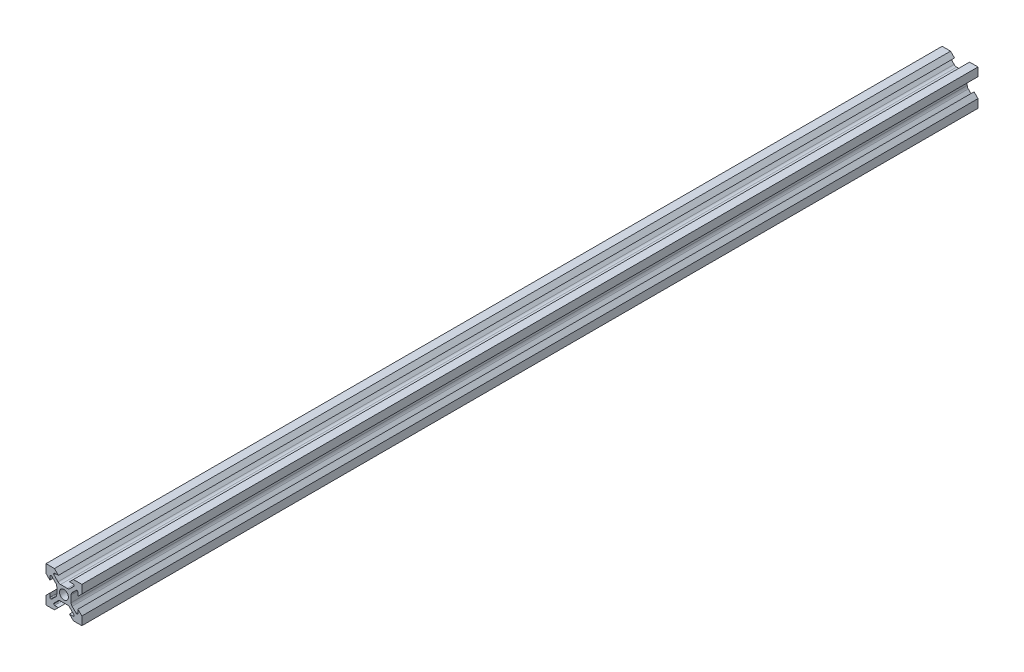
SolidWorks part; units mm, degrees
ref_plane "Front Plane" through (0, 0, 0) normal (0, 0, 1) x (1, 0, 0)
ref_plane "Top Plane" through (0, 0, 0) normal (0, 1, 0) x (1, 0, 0)
ref_plane "Right Plane" through (0, 0, 0) normal (1, 0, 0) x (0, 0, -1)
sketch "Sketch1" plane through (0, 0, 0) normal (0, 0, 1) x (1, 0, 0)
  line L0 (0, -10) -> (0, 10) construction
  line L1 (-10, 10) -> (10, 10) construction
  line L2 (-10, 10) -> (-10, -10) construction
  line L3 (-10, -10) -> (10, -10) construction
  line L4 (10, 10) -> (10, -10) construction
  line L5 (-10, 10) -> (10, -10) construction
  line L6 (-10, -10) -> (10, 10) construction
  line L7 (-10, 0) -> (10, 0) construction
  line L8 (-4, 0) -> (-4, 1.8988)
  line L9 (-4.5858, 3.313) -> (-6.8263, 5.5536)
  line L10 (-7.1799, 5.7) -> (-7.3, 5.7)
  line L11 (-7.8, 5.2) -> (-7.8, 3.1)
  line L12 (-7.8, 3.1) -> (-10, 5.3)
  line L13 (-10, 5.3) -> (-10, 10)
  line L14 (0, 4) -> (-1.8988, 4)
  line L15 (-3.313, 4.5858) -> (-5.5536, 6.8263)
  line L16 (-5.7, 7.1799) -> (-5.7, 7.3)
  line L17 (-5.2, 7.8) -> (-3.1, 7.8)
  line L18 (-3.1, 7.8) -> (-5.3, 10)
  line L19 (-5.3, 10) -> (-10, 10)
  line L20 (5.3, 10) -> (10, 10)
  line L21 (3.1, 7.8) -> (5.3, 10)
  line L22 (5.2, 7.8) -> (3.1, 7.8)
  line L23 (5.7, 7.1799) -> (5.7, 7.3)
  line L24 (3.313, 4.5858) -> (5.5536, 6.8263)
  line L25 (0, 4) -> (1.8988, 4)
  line L26 (10, -5.3) -> (10, -10)
  line L27 (7.8, -3.1) -> (10, -5.3)
  line L28 (7.8, -5.2) -> (7.8, -3.1)
  line L29 (7.1799, -5.7) -> (7.3, -5.7)
  line L30 (4.5858, -3.313) -> (6.8263, -5.5536)
  line L31 (4, 0) -> (4, -1.8988)
  line L32 (-5.3, -10) -> (-10, -10)
  line L33 (-3.1, -7.8) -> (-5.3, -10)
  line L34 (-5.2, -7.8) -> (-3.1, -7.8)
  line L35 (-5.7, -7.1799) -> (-5.7, -7.3)
  line L36 (-3.313, -4.5858) -> (-5.5536, -6.8263)
  line L37 (0, -4) -> (-1.8988, -4)
  line L38 (10, 5.3) -> (10, 10)
  line L39 (7.8, 3.1) -> (10, 5.3)
  line L40 (7.8, 5.2) -> (7.8, 3.1)
  line L41 (7.1799, 5.7) -> (7.3, 5.7)
  line L42 (4.5858, 3.313) -> (6.8263, 5.5536)
  line L43 (4, 0) -> (4, 1.8988)
  line L44 (5.3, -10) -> (10, -10)
  line L45 (3.1, -7.8) -> (5.3, -10)
  line L46 (5.2, -7.8) -> (3.1, -7.8)
  line L47 (5.7, -7.1799) -> (5.7, -7.3)
  line L48 (3.313, -4.5858) -> (5.5536, -6.8263)
  line L49 (0, -4) -> (1.8988, -4)
  line L50 (-10, -5.3) -> (-10, -10)
  line L51 (-7.8, -3.1) -> (-10, -5.3)
  line L52 (-7.8, -5.2) -> (-7.8, -3.1)
  line L53 (-7.1799, -5.7) -> (-7.3, -5.7)
  line L54 (-4.5858, -3.313) -> (-6.8263, -5.5536)
  line L55 (-4, 0) -> (-4, -1.8988)
  circle A0 centre (0, 0) radius 2.5
  arc A1 (-7.3, 5.7) -> (-7.8, 5.2) centre (-7.3, 5.2) ccw
  arc A2 (-6.8263, 5.5536) -> (-7.1799, 5.7) centre (-7.1799, 5.2) ccw
  arc A3 (-4, 1.8988) -> (-4.5858, 3.313) centre (-6, 1.8988) ccw
  arc A4 (-1.8988, 4) -> (-3.313, 4.5858) centre (-1.8988, 6) cw
  arc A5 (-5.5536, 6.8263) -> (-5.7, 7.1799) centre (-5.2, 7.1799) cw
  arc A6 (-5.7, 7.3) -> (-5.2, 7.8) centre (-5.2, 7.3) cw
  arc A7 (5.7, 7.3) -> (5.2, 7.8) centre (5.2, 7.3) ccw
  arc A8 (5.5536, 6.8263) -> (5.7, 7.1799) centre (5.2, 7.1799) ccw
  arc A9 (1.8988, 4) -> (3.313, 4.5858) centre (1.8988, 6) ccw
  arc A10 (7.3, -5.7) -> (7.8, -5.2) centre (7.3, -5.2) ccw
  arc A11 (6.8263, -5.5536) -> (7.1799, -5.7) centre (7.1799, -5.2) ccw
  arc A12 (4, -1.8988) -> (4.5858, -3.313) centre (6, -1.8988) ccw
  arc A13 (-5.7, -7.3) -> (-5.2, -7.8) centre (-5.2, -7.3) ccw
  arc A14 (-5.5536, -6.8263) -> (-5.7, -7.1799) centre (-5.2, -7.1799) ccw
  arc A15 (-1.8988, -4) -> (-3.313, -4.5858) centre (-1.8988, -6) ccw
  arc A16 (7.3, 5.7) -> (7.8, 5.2) centre (7.3, 5.2) cw
  arc A17 (6.8263, 5.5536) -> (7.1799, 5.7) centre (7.1799, 5.2) cw
  arc A18 (4, 1.8988) -> (4.5858, 3.313) centre (6, 1.8988) cw
  arc A19 (5.7, -7.3) -> (5.2, -7.8) centre (5.2, -7.3) cw
  arc A20 (5.5536, -6.8263) -> (5.7, -7.1799) centre (5.2, -7.1799) cw
  arc A21 (1.8988, -4) -> (3.313, -4.5858) centre (1.8988, -6) cw
  arc A22 (-7.3, -5.7) -> (-7.8, -5.2) centre (-7.3, -5.2) cw
  arc A23 (-6.8263, -5.5536) -> (-7.1799, -5.7) centre (-7.1799, -5.2) cw
  arc A24 (-4, -1.8988) -> (-4.5858, -3.313) centre (-6, -1.8988) cw
  dimension "D1" = 5
  dimension "D9" = 0.5
  dimension "D10" = 2
  dimension "D2" = 20
  dimension "D3" = 20
  dimension "D4" = 5.3
  dimension "D5" = 5.7
  dimension "D6" = 0.9
  dimension "D7" = 3.1
  dimension "D8" = 6
  dimension "D11" = 4
  dimension "D12" = 4
extrude "Boss-Extrude2" add sketch "Sketch1" along normal blind 500
